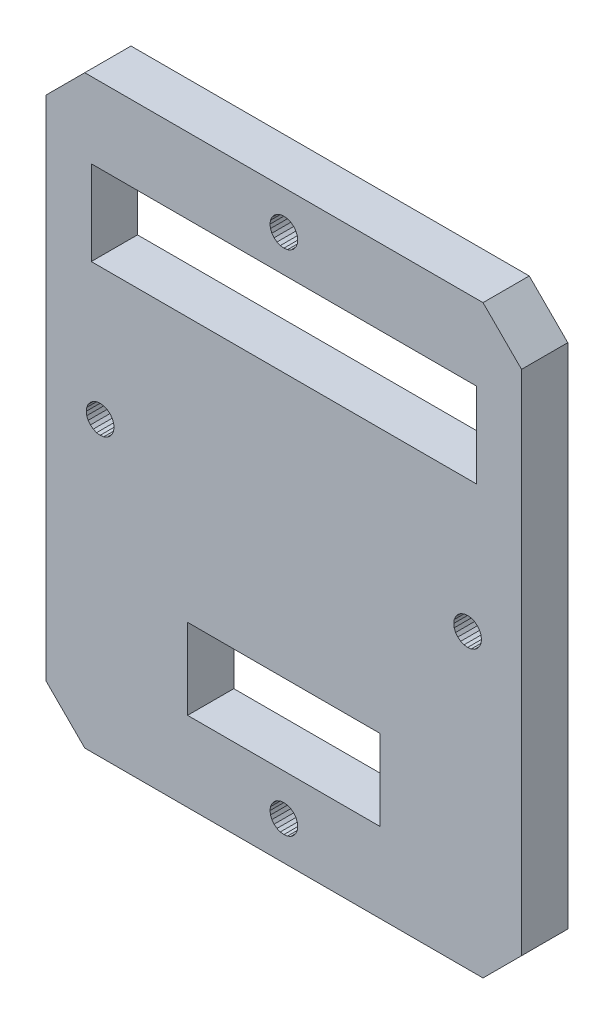
SolidWorks part; units mm, degrees
material "Maple"
ref_plane "Front Plane" through (0, 0, 0) normal (0, 0, 1) x (1, 0, 0)
ref_plane "Top Plane" through (0, 0, 0) normal (0, 1, 0) x (1, 0, 0)
ref_plane "Right Plane" through (0, 0, 0) normal (1, 0, 0) x (0, 0, -1)
sketch "Sketch1" plane through (0, 0, 0) normal (0, 0, 1) x (1, 0, 0)
  line L8 (-13.8696, 182.4161) -> (-65.562, 182.4161)
  line L160 (-27.2158, 203.2232) -> (-27.2158, 192.7661)
  line L161 (-27.2158, 192.7661) -> (-52.2158, 192.7661)
  line L162 (-70.562, 187.4161) -> (-65.562, 182.4161)
  line L163 (-8.8696, 187.4161) -> (-8.8696, 253.3303)
  line L164 (-13.8696, 182.4161) -> (-8.8696, 187.4161)
  line L165 (-70.562, 253.3303) -> (-70.562, 187.4161)
  line L166 (-70.562, 253.3303) -> (-65.562, 258.3303)
  line L167 (-13.8696, 258.3303) -> (-65.562, 258.3303)
  line L168 (-13.8696, 258.3303) -> (-8.8696, 253.3303)
  line L169 (-52.2158, 192.7661) -> (-52.2158, 203.2232)
  line L170 (-52.2158, 203.2232) -> (-27.2158, 203.2232)
  line L171 (-14.7158, 237.5232) -> (-64.7158, 237.5232)
  line L172 (-64.7158, 237.5232) -> (-64.7158, 248.5232)
  line L173 (-64.7158, 248.5232) -> (-14.7158, 248.5232)
  line L174 (-14.7158, 248.5232) -> (-14.7158, 237.5232)
  line L175 (-64.0279, 218.6345) -> (-63.562, 218.5732)
  line L176 (-64.462, 218.8144) -> (-64.0279, 218.6345)
  line L177 (-64.8348, 221.646) -> (-65.1209, 221.2732)
  line L178 (-64.462, 221.9321) -> (-64.8348, 221.646)
  line L179 (-64.0279, 222.1119) -> (-64.462, 221.9321)
  line L180 (-63.562, 222.1732) -> (-64.0279, 222.1119)
  line L181 (-65.1209, 219.4732) -> (-64.8348, 219.1004)
  line L182 (-65.3007, 219.9073) -> (-65.1209, 219.4732)
  line L183 (-65.362, 220.3732) -> (-65.3007, 219.9073)
  line L184 (-62.662, 221.9321) -> (-63.0961, 222.1119)
  line L185 (-62.2892, 219.1004) -> (-62.0032, 219.4732)
  line L186 (-65.3007, 220.8391) -> (-65.362, 220.3732)
  line L187 (-62.2892, 221.646) -> (-62.662, 221.9321)
  line L188 (-62.0032, 221.2732) -> (-62.2892, 221.646)
  line L189 (-61.8234, 220.8391) -> (-62.0032, 221.2732)
  line L190 (-61.762, 220.3732) -> (-61.8234, 220.8391)
  line L191 (-61.8234, 219.9073) -> (-61.762, 220.3732)
  line L192 (-62.0032, 219.4732) -> (-61.8234, 219.9073)
  line L193 (-62.662, 218.8144) -> (-62.2892, 219.1004)
  line L194 (-63.0961, 218.6345) -> (-62.662, 218.8144)
  line L195 (-63.562, 218.5732) -> (-63.0961, 218.6345)
  line L196 (-65.1209, 221.2732) -> (-65.3007, 220.8391)
  line L197 (-64.8348, 219.1004) -> (-64.462, 218.8144)
  line L198 (-63.0961, 222.1119) -> (-63.562, 222.1732)
  line L199 (-15.8696, 222.1732) -> (-16.3355, 222.1119)
  line L200 (-17.6083, 220.8391) -> (-17.6696, 220.3732)
  line L201 (-16.3355, 222.1119) -> (-16.7696, 221.9321)
  line L202 (-16.7696, 221.9321) -> (-17.1424, 221.646)
  line L203 (-17.1424, 221.646) -> (-17.4284, 221.2732)
  line L204 (-17.4284, 221.2732) -> (-17.6083, 220.8391)
  line L205 (-16.7696, 218.8144) -> (-16.3355, 218.6345)
  line L206 (-16.3355, 218.6345) -> (-15.8696, 218.5732)
  line L207 (-17.1424, 219.1004) -> (-16.7696, 218.8144)
  line L208 (-14.9696, 221.9321) -> (-15.4037, 222.1119)
  line L209 (-14.5968, 219.1004) -> (-14.3107, 219.4732)
  line L210 (-14.5968, 221.646) -> (-14.9696, 221.9321)
  line L211 (-14.3107, 221.2732) -> (-14.5968, 221.646)
  line L212 (-14.1309, 220.8391) -> (-14.3107, 221.2732)
  line L213 (-14.0696, 220.3732) -> (-14.1309, 220.8391)
  line L214 (-14.1309, 219.9073) -> (-14.0696, 220.3732)
  line L215 (-15.4037, 222.1119) -> (-15.8696, 222.1732)
  line L216 (-14.3107, 219.4732) -> (-14.1309, 219.9073)
  line L217 (-15.8696, 218.5732) -> (-15.4037, 218.6345)
  line L218 (-15.4037, 218.6345) -> (-14.9696, 218.8144)
  line L219 (-14.9696, 218.8144) -> (-14.5968, 219.1004)
  line L220 (-17.6696, 220.3732) -> (-17.6083, 219.9073)
  line L221 (-17.6083, 219.9073) -> (-17.4284, 219.4732)
  line L222 (-17.4284, 219.4732) -> (-17.1424, 219.1004)
  line L223 (-37.9771, 187.882) -> (-38.157, 188.3161)
  line L224 (-37.9158, 187.4161) -> (-37.9771, 187.882)
  line L225 (-37.9771, 186.9502) -> (-37.9158, 187.4161)
  line L226 (-38.157, 186.5161) -> (-37.9771, 186.9502)
  line L227 (-38.8158, 185.8572) -> (-38.443, 186.1433)
  line L228 (-39.2499, 185.6774) -> (-38.8158, 185.8572)
  line L229 (-39.7158, 185.6161) -> (-39.2499, 185.6774)
  line L230 (-41.2747, 188.3161) -> (-41.4545, 187.882)
  line L231 (-40.9886, 186.1433) -> (-40.6158, 185.8572)
  line L232 (-39.2499, 189.1547) -> (-39.7158, 189.2161)
  line L233 (-40.6158, 188.9749) -> (-40.9886, 188.6889)
  line L234 (-40.1817, 189.1547) -> (-40.6158, 188.9749)
  line L235 (-39.7158, 189.2161) -> (-40.1817, 189.1547)
  line L236 (-41.2747, 186.5161) -> (-40.9886, 186.1433)
  line L237 (-41.4545, 186.9502) -> (-41.2747, 186.5161)
  line L238 (-41.5158, 187.4161) -> (-41.4545, 186.9502)
  line L239 (-38.8158, 188.9749) -> (-39.2499, 189.1547)
  line L240 (-38.443, 186.1433) -> (-38.157, 186.5161)
  line L241 (-41.4545, 187.882) -> (-41.5158, 187.4161)
  line L242 (-38.443, 188.6889) -> (-38.8158, 188.9749)
  line L243 (-38.157, 188.3161) -> (-38.443, 188.6889)
  line L244 (-40.9886, 188.6889) -> (-41.2747, 188.3161)
  line L245 (-40.1817, 185.6774) -> (-39.7158, 185.6161)
  line L246 (-40.6158, 185.8572) -> (-40.1817, 185.6774)
  line L247 (-37.9771, 252.8645) -> (-37.9158, 253.3303)
  line L248 (-39.2499, 251.5917) -> (-38.8158, 251.7715)
  line L249 (-38.8158, 251.7715) -> (-38.443, 252.0575)
  line L250 (-38.443, 252.0575) -> (-38.157, 252.4303)
  line L251 (-38.157, 252.4303) -> (-37.9771, 252.8645)
  line L252 (-37.9771, 253.7962) -> (-38.157, 254.2303)
  line L253 (-37.9158, 253.3303) -> (-37.9771, 253.7962)
  line L254 (-41.2747, 254.2303) -> (-41.4545, 253.7962)
  line L255 (-40.9886, 252.0575) -> (-40.6158, 251.7715)
  line L256 (-39.2499, 255.069) -> (-39.7158, 255.1303)
  line L257 (-41.5158, 253.3303) -> (-41.4545, 252.8645)
  line L258 (-41.4545, 252.8645) -> (-41.2747, 252.4303)
  line L259 (-41.2747, 252.4303) -> (-40.9886, 252.0575)
  line L260 (-40.6158, 251.7715) -> (-40.1817, 251.5917)
  line L261 (-40.1817, 251.5917) -> (-39.7158, 251.5303)
  line L262 (-39.7158, 251.5303) -> (-39.2499, 251.5917)
  line L263 (-40.9886, 254.6031) -> (-41.2747, 254.2303)
  line L264 (-38.157, 254.2303) -> (-38.443, 254.6031)
  line L265 (-38.443, 254.6031) -> (-38.8158, 254.8892)
  line L266 (-38.8158, 254.8892) -> (-39.2499, 255.069)
  line L267 (-40.6158, 254.8892) -> (-40.9886, 254.6031)
  line L268 (-40.1817, 255.069) -> (-40.6158, 254.8892)
  line L269 (-39.7158, 255.1303) -> (-40.1817, 255.069)
  line L270 (-41.4545, 253.7962) -> (-41.5158, 253.3303)
  line L8470 (-41.9948, 217.758) -> (-41.9948, 222.0659)
  line L8471 (-41.9948, 222.0659) -> (-39.8344, 217.758)
  line L8472 (-39.8344, 217.758) -> (-39.8344, 222.0659)
  line L8473 (-39.8344, 222.0659) -> (-39.8344, 217.758)
  line L8474 (-39.8344, 217.758) -> (-41.9948, 222.0659)
  line L8475 (-41.9948, 222.0659) -> (-41.9948, 217.758)
  line L8476 (-39.0041, 217.758) -> (-39.0041, 219.5624)
  line L8477 (-39.0041, 219.5624) -> (-38.9694, 219.6771)
  line L8478 (-38.9694, 219.6771) -> (-38.8839, 219.7777)
  line L8479 (-38.8839, 219.7777) -> (-38.5608, 219.9369)
  line L8480 (-38.5608, 219.9369) -> (-38.2268, 219.9775)
  line L8481 (-38.2268, 219.9775) -> (-37.9052, 220.0368)
  line L8482 (-37.9052, 220.0368) -> (-37.4463, 220.118)
  line L8483 (-37.4463, 220.118) -> (-37.1372, 220.1992)
  line L8484 (-37.1372, 220.1992) -> (-36.8469, 220.3631)
  line L8485 (-36.8469, 220.3631) -> (-36.7743, 220.4602)
  line L8486 (-36.7743, 220.4602) -> (-36.7501, 220.5675)
  line L8487 (-36.7501, 220.5675) -> (-36.7501, 221.5852)
  line L8488 (-36.7501, 221.5852) -> (-36.7702, 221.6814)
  line L8489 (-36.7702, 221.6814) -> (-36.8305, 221.7701)
  line L8490 (-36.8305, 221.7701) -> (-37.0716, 221.9255)
  line L8491 (-37.0716, 221.9255) -> (-37.433, 222.0308)
  line L8492 (-37.433, 222.0308) -> (-37.874, 222.0659)
  line L8493 (-37.874, 222.0659) -> (-38.315, 222.0308)
  line L8494 (-38.315, 222.0308) -> (-38.6763, 221.9255)
  line L8495 (-38.6763, 221.9255) -> (-38.9175, 221.7701)
  line L8496 (-38.9175, 221.7701) -> (-38.9778, 221.6814)
  line L8497 (-38.9778, 221.6814) -> (-38.9979, 221.5852)
  line L8498 (-38.9979, 221.5852) -> (-38.9979, 221.2793)
  line L8499 (-38.9979, 221.2793) -> (-38.9979, 221.5852)
  line L8500 (-38.9979, 221.5852) -> (-38.9778, 221.6814)
  line L8501 (-38.9778, 221.6814) -> (-38.9175, 221.7701)
  line L8502 (-38.9175, 221.7701) -> (-38.6763, 221.9255)
  line L8503 (-38.6763, 221.9255) -> (-38.315, 222.0308)
  line L8504 (-38.315, 222.0308) -> (-37.874, 222.0659)
  line L8505 (-37.874, 222.0659) -> (-37.433, 222.0308)
  line L8506 (-37.433, 222.0308) -> (-37.0716, 221.9255)
  line L8507 (-37.0716, 221.9255) -> (-36.8305, 221.7701)
  line L8508 (-36.8305, 221.7701) -> (-36.7702, 221.6814)
  line L8509 (-36.7702, 221.6814) -> (-36.7501, 221.5852)
  line L8510 (-36.7501, 221.5852) -> (-36.7501, 220.5675)
  line L8511 (-36.7501, 220.5675) -> (-36.7743, 220.4602)
  line L8512 (-36.7743, 220.4602) -> (-36.8469, 220.3631)
  line L8513 (-36.8469, 220.3631) -> (-37.1372, 220.1992)
  line L8514 (-37.1372, 220.1992) -> (-37.4463, 220.118)
  line L8515 (-37.4463, 220.118) -> (-37.9052, 220.0368)
  line L8516 (-37.9052, 220.0368) -> (-38.2268, 219.9775)
  line L8517 (-38.2268, 219.9775) -> (-38.5608, 219.9369)
  line L8518 (-38.5608, 219.9369) -> (-38.8839, 219.7777)
  line L8519 (-38.8839, 219.7777) -> (-38.9694, 219.6771)
  line L8520 (-38.9694, 219.6771) -> (-39.0041, 219.5624)
  line L8521 (-39.0041, 219.5624) -> (-39.0041, 217.758)
  line L8522 (-39.0041, 217.758) -> (-36.8687, 217.758)
  line L8523 (-36.8687, 217.758) -> (-39.0041, 217.758)
extrude "Boss-Extrude1" add sketch "Sketch1" along normal blind 6
